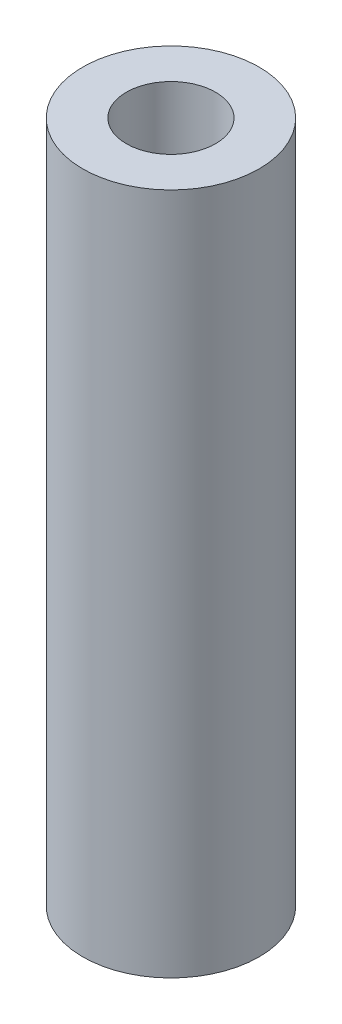
SolidWorks part; units mm, degrees
ref_plane "Front Plane" through (0, 0, 0) normal (0, 0, 1) x (1, 0, 0)
ref_plane "Top Plane" through (0, 0, 0) normal (0, 1, 0) x (1, 0, 0)
ref_plane "Right Plane" through (0, 0, 0) normal (1, 0, 0) x (0, 0, -1)
sketch "Sketch1" plane through (0, 0, 0) normal (0, 1, 0) x (1, 0, 0)
  circle A0 centre (0, 0) radius 6.15
  dimension "D1" = 12.3
extrude "Extrude-Thin1" add sketch "Sketch1" along normal blind 94 thin
